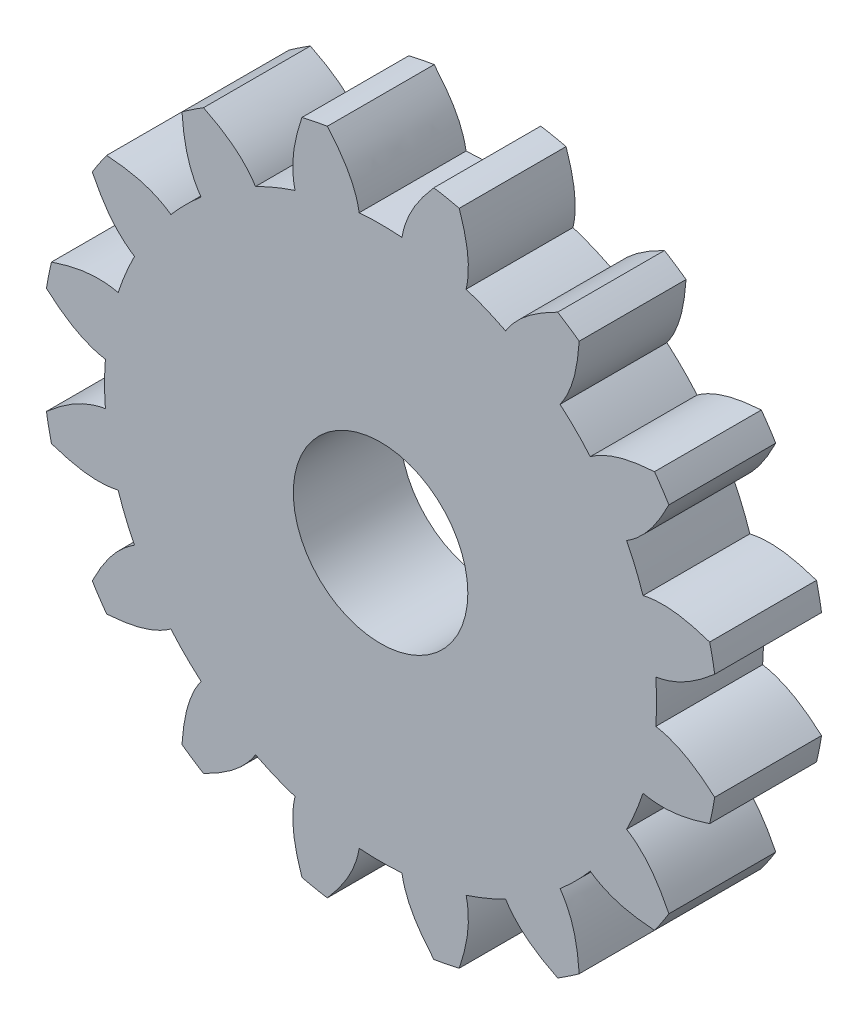
SolidWorks part; units mm, degrees
ref_plane "Front Plane" through (0, 0, 0) normal (0, 0, 1) x (1, 0, 0)
ref_plane "Top Plane" through (0, 0, 0) normal (0, 1, 0) x (1, 0, 0)
ref_plane "Right Plane" through (0, 0, 0) normal (1, 0, 0) x (0, 0, -1)
sketch "Sketch1" plane through (0, 0, 0) normal (0, 0, 1) x (1, 0, 0)
  circle A0 centre (0, 0) radius 2.45
  circle A1 centre (0, 0) radius 9.5
  dimension "D1" = 4.9
  dimension "D2" = 19
extrude "Boss-Extrude1" add sketch "Sketch1" along normal blind 3
sketch "Sketch6" plane through (0, 0, 0) normal (0, 0, -1) x (-1, 0, 0)
  line L0 (0, 9.5) -> (0, -9.5) construction
  line L1 (9.5, 0) -> (-9.5, 0) construction
  circle A0 centre (0, 0) radius 7.75
  circle A1 centre (0, 0) radius 9.5 construction
  spline S0 degree 3 poles (1.4953, 9.3816) (1.0368, 8.8535) (0.7053, 8.3496) (0.6, 7.7267) knots 0 0 0 0 1 1 1 1
  spline S1 degree 3 poles (-1.4953, 9.3816) (-1.0368, 8.8535) (-0.7053, 8.3496) (-0.6, 7.7267) knots 0 0 0 0 1 1 1 1
  spline S3 degree 2 poles (-0.6, 7.7267) (0, 7.7733) (0.6, 7.7267) knots 0 0 0 1 1 1
  dimension "D1" = 1.75
  dimension "D2" = 0.6
  dimension "D4" = 1.5
extrude "Cut-Extrude1" cut sketch "Sketch6" against normal blind 10
pattern_circular "CirPattern1" count 16 over 360 about axis through (0, 0, 0) along (0, 0, 1) of "Cut-Extrude1"
